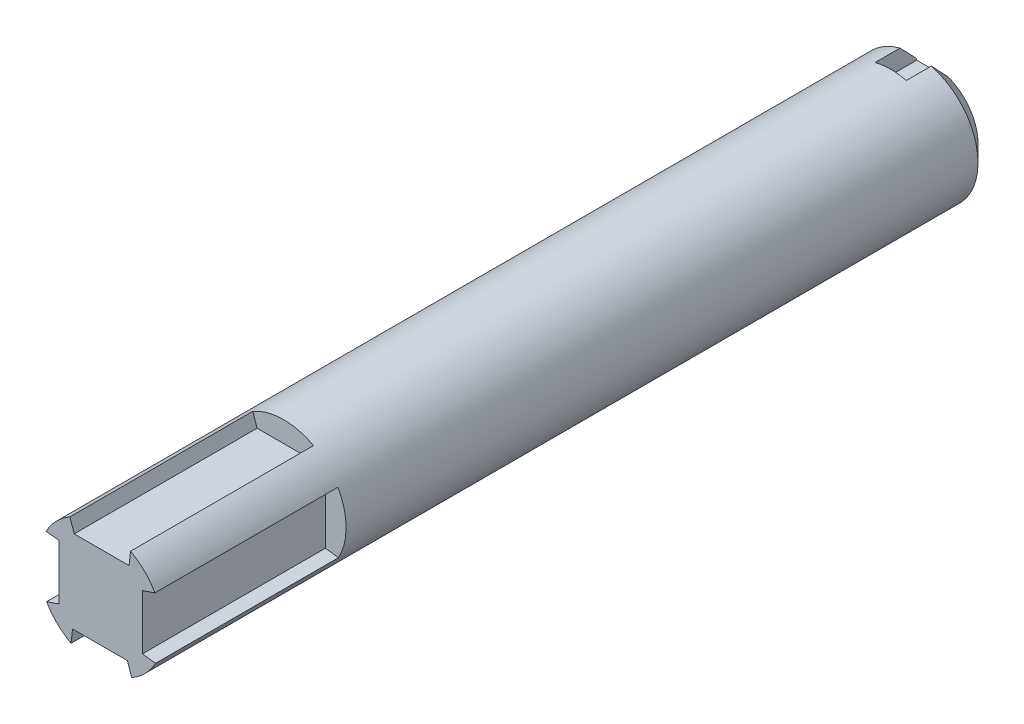
SolidWorks part; units mm, degrees
ref_plane "Front Plane" through (0, 0, 0) normal (0, 0, 1) x (1, 0, 0)
ref_plane "Top Plane" through (0, 0, 0) normal (0, 1, 0) x (1, 0, 0)
ref_plane "Right Plane" through (0, 0, 0) normal (1, 0, 0) x (0, 0, -1)
sketch "Sketch1" plane through (0, 0, 0) normal (0, 0, 1) x (1, 0, 0)
  circle A0 centre (0, 0) radius 9.525
  dimension "D1" = 19.05
extrude "Boss-Extrude1" add sketch "Sketch1" against normal blind 127
sketch "Sketch2" plane through (0, 0, -127) normal (0, 0, -1) x (-1, 0, 0)
  line L0 (-9.525, 0) -> (9.525, 0) construction
  line L1 (0, -9.525) -> (0, 9.525) construction
  line L7 (-2.3813, 6.35) -> (2.3813, 6.35)
  line L8 (-2.3813, 6.35) -> (-2.3813, 9.525)
  line L9 (-2.3813, 9.525) -> (2.3813, 9.525)
  line L10 (2.3813, 6.35) -> (2.3813, 9.525)
  line L11 (-2.3813, 6.35) -> (2.3813, 9.525) construction
  line L12 (-2.3813, 9.525) -> (2.3813, 6.35) construction
  circle A0 centre (0, 0) radius 9.525 construction
  point P7 (0, 7.9375)
  point P12 (0, 9.525)
  dimension "D1" = 4.7625
  dimension "D2" = 3.175
extrude "Cut-Extrude1" cut sketch "Sketch2" against normal blind 6.35
chamfer "Chamfer1" distance 2.54 angle 45 1 edges at (0, -9.525, -127)
sketch "Sketch3" plane through (0, 0, 0) normal (0, 0, 1) x (1, 0, 0)
  line L0 (-9.525, 0) -> (9.525, 0) construction
  line L1 (0, 9.525) -> (0, -9.525) construction
  line L2 (-4.7204, 8.2731) -> (-4.064, 6.35)
  line L3 (-4.064, 6.35) -> (4.318, 6.35)
  line L4 (4.318, 6.35) -> (4.5483, 8.3689)
  line L5 (8.2731, 4.7204) -> (6.35, 4.064)
  line L6 (6.35, 4.064) -> (6.35, -4.318)
  line L7 (6.35, -4.318) -> (8.3689, -4.5483)
  line L8 (4.7204, -8.2731) -> (4.064, -6.35)
  line L9 (4.064, -6.35) -> (-4.318, -6.35)
  line L10 (-4.318, -6.35) -> (-4.5483, -8.3689)
  line L11 (-8.2731, -4.7204) -> (-6.35, -4.064)
  line L12 (-6.35, -4.064) -> (-6.35, 4.318)
  line L13 (-6.35, 4.318) -> (-8.3689, 4.5483)
  circle A0 centre (0, 0) radius 9.525 construction
  arc A2 (4.5483, 8.3689) -> (-4.7204, 8.2731) centre (0, 0) ccw
  arc A3 (8.3689, -4.5483) -> (8.2731, 4.7204) centre (0, 0) ccw
  arc A4 (-4.5483, -8.3689) -> (4.7204, -8.2731) centre (0, 0) ccw
  arc A5 (-8.3689, 4.5483) -> (-8.2731, -4.7204) centre (0, 0) ccw
  point P9 (0.127, 6.35)
  point P30 (0, 0)
  dimension "D1" = 8.382
  dimension "D2" = 2.032
  dimension "D3" = 2.032
  dimension "D4" = 6.35
  dimension "D5" = 4.064
  dimension "D6" = 4
extrude "Cut-Extrude2" cut sketch "Sketch3" against normal blind 27.94
